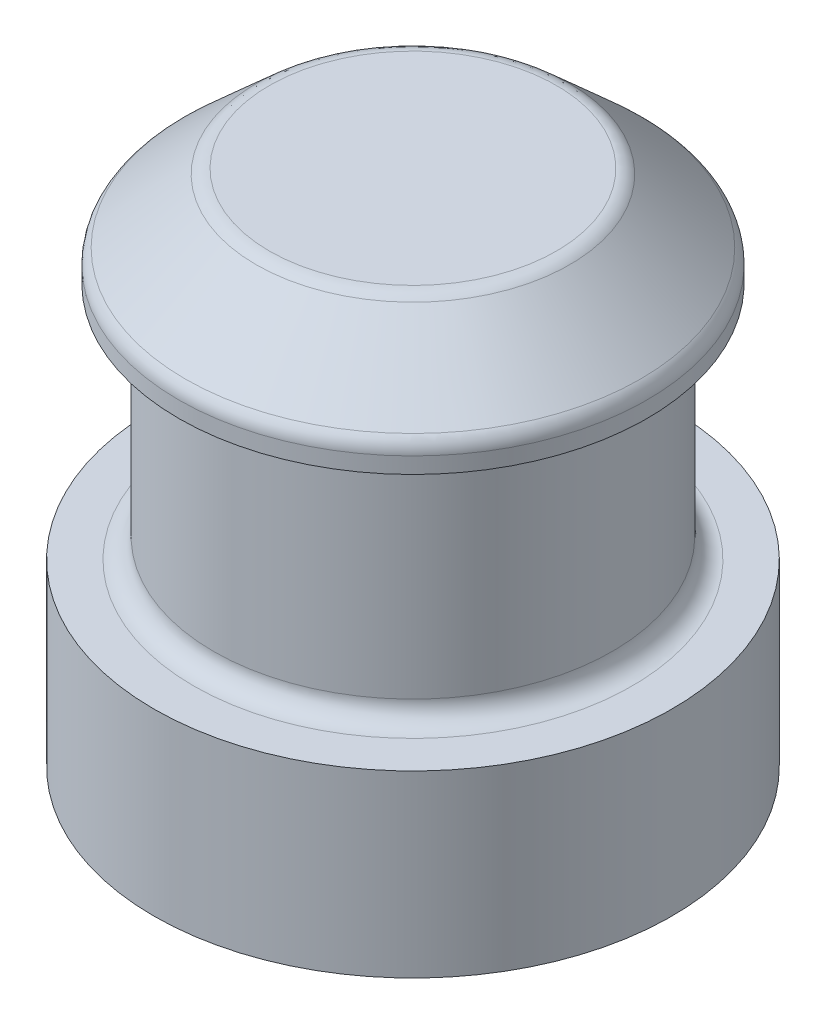
SolidWorks part; units mm, degrees
ref_plane "Front Plane" through (0, 0, 0) normal (0, 0, 1) x (1, 0, 0)
ref_plane "Top Plane" through (0, 0, 0) normal (0, 1, 0) x (1, 0, 0)
ref_plane "Right Plane" through (0, 0, 0) normal (1, 0, 0) x (0, 0, -1)
sketch "Sketch1" plane through (0, 0, 0) normal (0, 1, 0) x (1, 0, 0)
  line L5 (7, -7) -> (-7, 7) construction
  line L6 (7, 7) -> (-7, -7) construction
  circle A0 centre (0, 0) radius 2.6
  point P0 (0, 0)
  dimension "D3" = 5.2
  dimension "D1" = 14
  dimension "D2" = 14
extrude "Boss-Extrude1" add sketch "Sketch1" along normal blind 1.8
ref_plane "Plane1" through (0, 1.8, 0) normal (0, 1, 0) x (1, 0, 0)
sketch "Sketch2" plane through (0, 1.8, 0) normal (0, 1, 0) x (1, 0, 0)
  circle A0 centre (0, 0) radius 2
extrude "Boss-Extrude2" add sketch "Sketch2" along normal blind 2.4
ref_plane "Plane2" through (0, 4.2, 0) normal (0, 1, 0) x (1, 0, 0)
sketch "Sketch3" plane through (0, 4.2, 0) normal (0, 1, 0) x (1, 0, 0)
  circle A0 centre (0, 0) radius 2.35
  circle A1 centre (0, 0) radius 2 construction
extrude "Boss-Extrude3" add sketch "Sketch3" along normal blind 1
chamfer "Chamfer1" distance 0.75 angle 48 1 edges at (0, 5.2, 2.35)
fillet "Fillet1" radius 0.2 3 edges at (0, 5.2, 1.517) (0, 4.45, 2.35) (0, 1.8, 2)
scale "Scale1" scale about centroid uniform scaling yes scale factor 1.15
